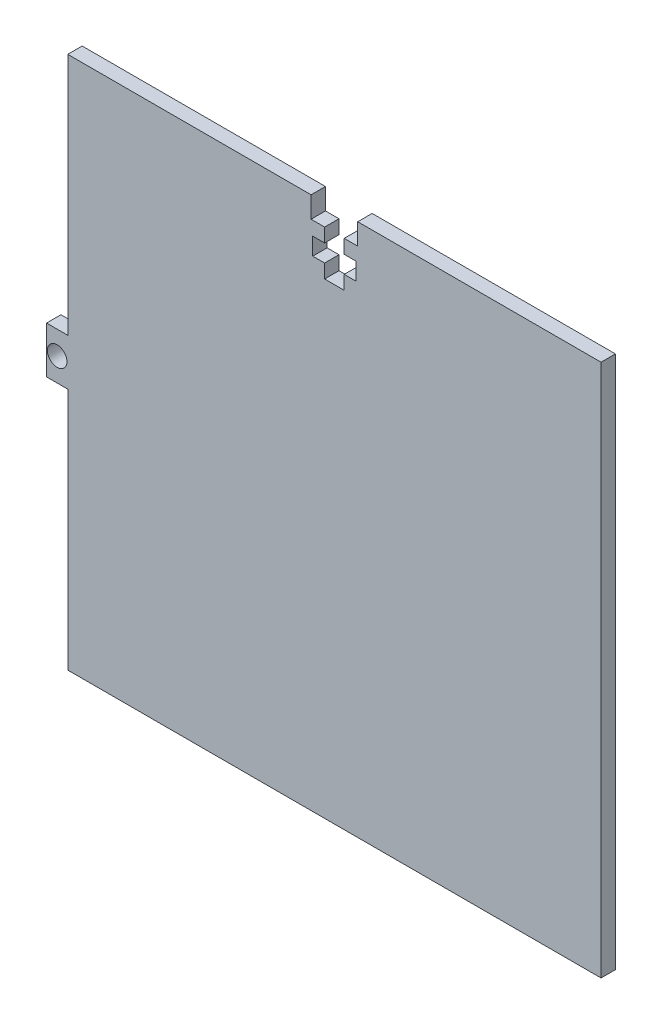
SolidWorks part; units mm, degrees
ref_plane "Front Plane" through (0, 0, 0) normal (0, 0, 1) x (1, 0, 0)
ref_plane "Top Plane" through (0, 0, 0) normal (0, 1, 0) x (1, 0, 0)
ref_plane "Right Plane" through (0, 0, 0) normal (1, 0, 0) x (0, 0, -1)
sketch "Sketch1" plane through (0, 0, 0) normal (0, 0, 1) x (1, 0, 0)
  line L1 (-40, 40) -> (40, 40)
  line L2 (-40, 40) -> (-40, -40)
  line L3 (-40, -40) -> (40, -40)
  line L4 (40, 40) -> (40, -40)
  line L5 (-40, 40) -> (40, -40) construction
  line L6 (-40, -40) -> (40, 40) construction
  point P0 (0, 0)
  dimension "D1" = 80
extrude "Boss-Extrude1" add sketch "Sketch1" along normal blind 2.1588
sketch "Sketch2" plane through (0, 0, 2.1588) normal (0, 0, 1) x (1, 0, 0)
  line L0 (0, 0) -> (0, 40) construction
  line L1 (40, 40) -> (-40, 40) construction
  line L3 (-3.5, 40) -> (3.5, 40)
  line L4 (-3.5, 40) -> (-3.5, 36.825)
  line L5 (-3.5, 36.825) -> (3.5, 36.825)
  line L6 (3.5, 40) -> (3.5, 36.825)
  dimension "D1" = 3.175
  dimension "D2" = 7
extrude "Cut-Extrude1" cut sketch "Sketch2" against normal through all
sketch "Sketch3" plane through (0, 0, 2.1588) normal (0, 0, 1) x (1, 0, 0)
  line L0 (0, 36.825) -> (0, 30.075) construction
  line L1 (-3.5, 36.825) -> (3.5, 36.825) construction
  line L2 (1.47, 34.75) -> (3.25, 34.75)
  line L3 (-1.47, 36.825) -> (1.47, 36.825)
  line L4 (-1.47, 36.825) -> (-1.47, 34.75)
  line L5 (-1.47, 30.075) -> (1.47, 30.075)
  line L6 (1.47, 36.825) -> (1.47, 34.75)
  line L7 (-3.25, 34.75) -> (-1.47, 34.75)
  line L8 (-3.25, 34.75) -> (-3.25, 32.15)
  line L9 (-3.25, 32.15) -> (-1.47, 32.15)
  line L10 (3.25, 34.75) -> (3.25, 32.15)
  line L11 (-1.47, 32.15) -> (-1.47, 30.075)
  line L12 (1.47, 32.15) -> (3.25, 32.15)
  line L13 (1.47, 32.15) -> (1.47, 30.075)
  line L14 (-3.5, 40) -> (-3.5, 36.825) construction
  line L15 (3.5, 36.825) -> (3.5, 40) construction
  line L16 (-1.6825, 32.15) -> (2.1415, 32.15) construction
  dimension "D1" = 2.6
  dimension "D2" = 6.5
  dimension "D3" = 2.94
  dimension "D5" = 2.075
  dimension "D4" = 6.75
extrude "Cut-Extrude2" cut sketch "Sketch3" against normal through all
sketch "Sketch4" plane through (0, 0, 2.1588) normal (0, 0, 1) x (1, 0, 0)
  line L0 (-40, 40) -> (-40, -40) construction
  line L1 (-40, 3.5) -> (-43.18, 3.5)
  line L2 (-40, 3.5) -> (-40, -3.5)
  line L3 (-40, -3.5) -> (-43.18, -3.5)
  line L4 (-43.18, 3.5) -> (-43.18, -3.5)
  line L5 (40, 0) -> (-40, 0) construction
  line L6 (40, -40) -> (40, 40) construction
  line L7 (-41.59, 3.5) -> (-41.59, -3.5) construction
  circle A0 centre (-41.59, 0) radius 1.47
  dimension "D3" = 2.94
  dimension "D1" = 3.18
  dimension "D2" = 7
extrude "Boss-Extrude2" add sketch "Sketch4" against normal up to surface (2.1588 mm away) up to face at (0, 27.7525, 0)
sketch "Sketch5" plane through (0, 0, 2.1588) normal (0, 0, 1) x (1, 0, 0)
  line L0 (-40.0395, -3.471) -> (-40.0395, 4.04) construction
  circle A1 centre (-41.59, 0) radius 1.47 construction
  dimension "D1" = 1.5505
equation "\"D5@Sketch3\"=(\"D4@Sketch3\"-2.6)/2"
